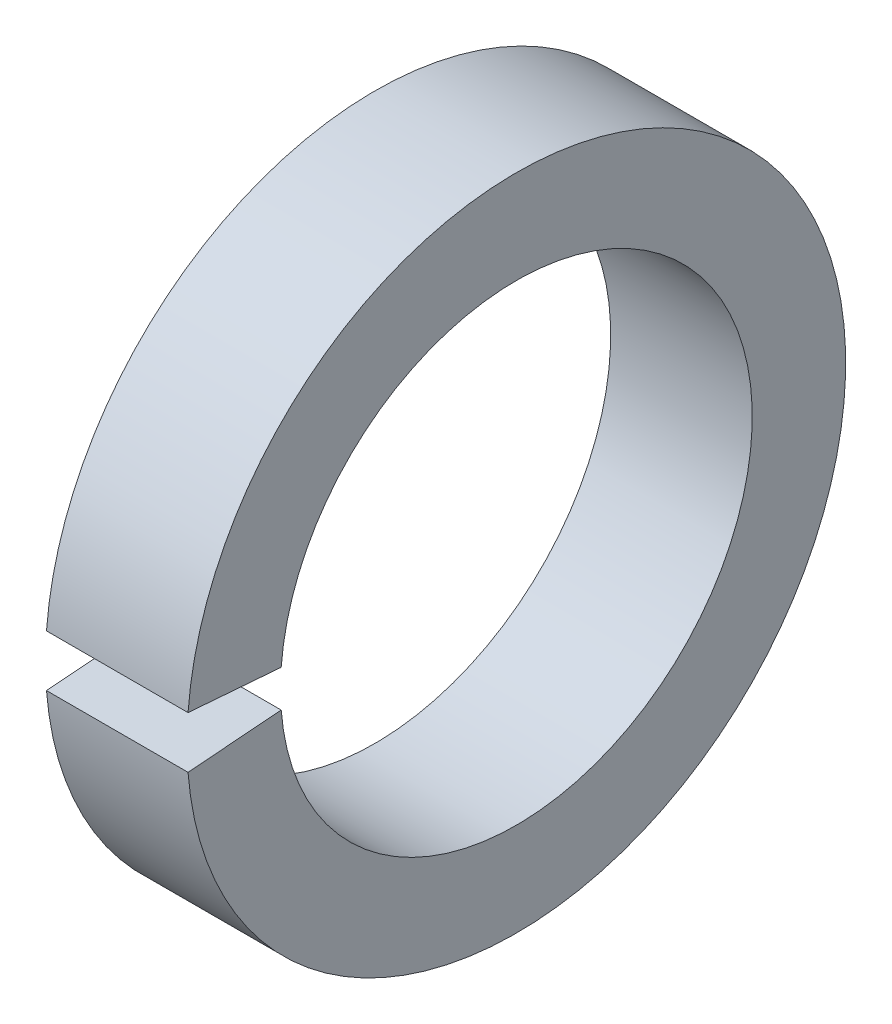
SolidWorks part; units mm, degrees
ref_plane "Plane1" through (0, 0, 0) normal (0, 0, 1) x (1, 0, 0)
ref_plane "Plane2" through (0, 0, 0) normal (0, 1, 0) x (1, 0, 0)
ref_plane "Plane3" through (0, 0, 0) normal (1, 0, 0) x (0, 0, -1)
other "Configuration Table"
sketch "Sketch1" plane through (0, 0, 0) normal (0, 0, 1) x (1, 0, 0)
  line L0 (-34.925, 0) -> (9.525, 0) construction
  line L1 (0, 3.302) -> (0, 4.6101)
  line L2 (0, 4.6101) -> (-1.9812, 4.6101)
  line L3 (-1.9812, 4.6101) -> (-1.9812, 3.302)
  line L4 (-1.9812, 3.302) -> (0, 3.302)
  dimension "Thickness" = 1.9812
  dimension "Inside_dia" = 6.604
  dimension "Outside_dia" = 9.2202
revolve "Base-Revolve" add sketch "Sketch1" angle 360 about L0
sketch "Sketch2" plane through (0, 0, 0) normal (-1, 0, 0) x (0, -1, 0)
  line L0 (0, 0) -> (0.3689, 4.6878)
  line L1 (0, -3.175) -> (0, 12.7) construction
  line L2 (0, 0) -> (-0.3689, 4.6878)
  arc A0 (0.3689, 4.6878) -> (-0.3689, 4.6878) centre (0, 0) ccw
  dimension "Gap_ang" = 9
  dimension "D1" = 4.7023
extrude "Gap" cut sketch "Sketch2" along normal through all
equation "\"D1@Sketch2\" = \"Outside_dia@Sketch1\" * 0.51"
